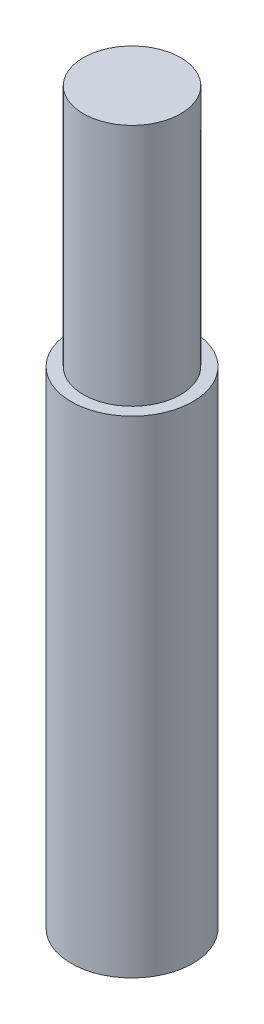
SolidWorks part; units mm, degrees
ref_plane "Ön Düzlem" through (0, 0, 0) normal (0, 0, 1) x (1, 0, 0)
ref_plane "Üst Düzlem" through (0, 0, 0) normal (0, 1, 0) x (1, 0, 0)
ref_plane "Sağ Düzlem" through (0, 0, 0) normal (1, 0, 0) x (0, 0, -1)
sketch "Çizim1" plane through (0, 0, 0) normal (0, 0, 1) x (1, 0, 0)
  line L0 (0, 0) -> (0, 30)
  line L1 (0, 30) -> (2, 30)
  line L2 (2, 30) -> (2, 20)
  line L3 (2, 20) -> (2.5, 20)
  line L4 (2.5, 20) -> (2.5, 0)
  line L5 (2.5, 0) -> (0, 0)
  dimension "D1" = 30
  dimension "D2" = 2
  dimension "D3" = 2.5
  dimension "D4" = 20
revolve "Döndür1" add sketch "Çizim1" angle 360 about L0
sketch "Çizim2" plane through (0, 0, 0) normal (0, -1, 0) x (1, 0, 0)
  circle A0 centre (0, 0) radius 2
  dimension "D1" = 4
extrude "Kes-Ekstrüzyon1" cut sketch "Çizim2" against normal blind 10
fillet "Radyus1" radius 0.4 1 edges at (0, 0, -2)
